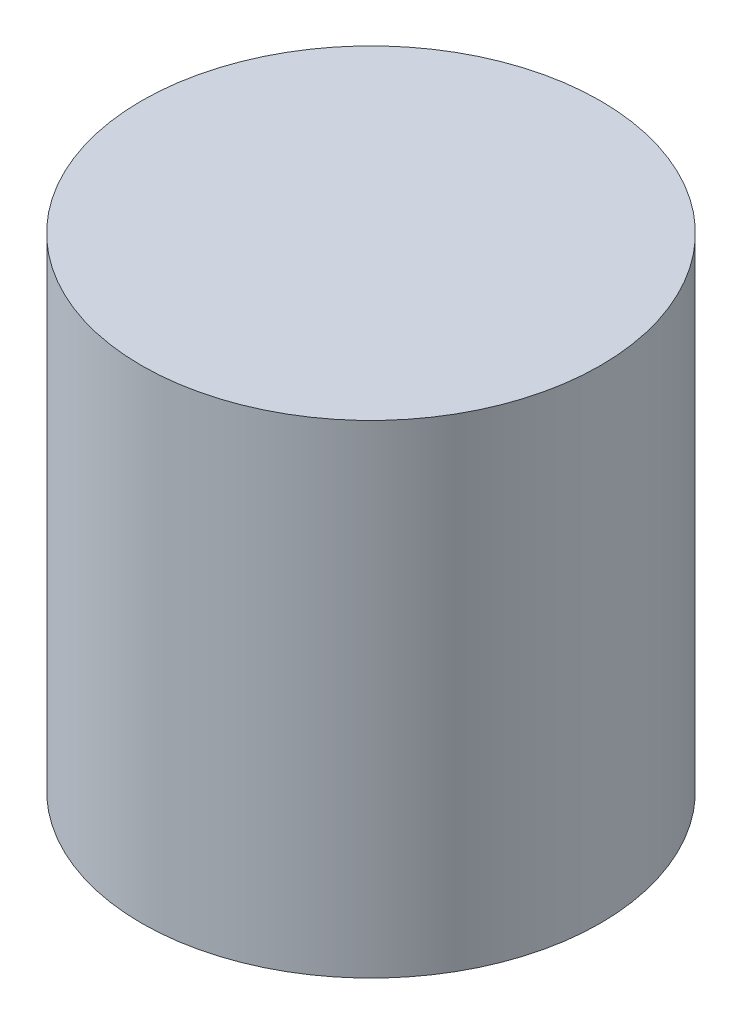
SolidWorks part; units mm, degrees
ref_plane "Front Plane" through (0, 0, 0) normal (0, 0, 1) x (1, 0, 0)
ref_plane "Top Plane" through (0, 0, 0) normal (0, 1, 0) x (1, 0, 0)
ref_plane "Right Plane" through (0, 0, 0) normal (1, 0, 0) x (0, 0, -1)
sketch "Sketch1" plane through (0, 0, 0) normal (0, 1, 0) x (1, 0, 0)
  circle A0 centre (-78.9891, -92.5261) radius 24.13
  dimension "D1" = 48.26
extrude "Boss-Extrude2" add sketch "Sketch1" along normal blind 50.8
